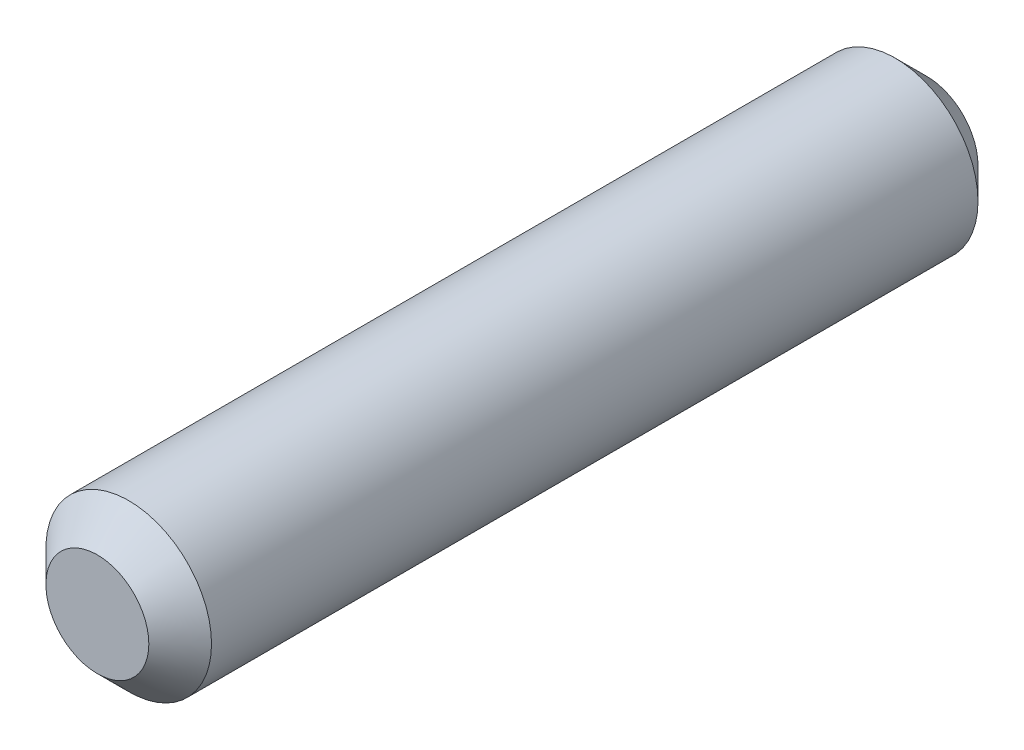
SolidWorks part; units mm, degrees
ref_plane "Front Plane" through (0, 0, 0) normal (0, 0, 1) x (1, 0, 0)
ref_plane "Top Plane" through (0, 0, 0) normal (0, 1, 0) x (1, 0, 0)
ref_plane "Right Plane" through (0, 0, 0) normal (1, 0, 0) x (0, 0, -1)
sketch "Sketch2" plane through (0, 0, 0) normal (0, 0, 1) x (1, 0, 0)
  circle A0 centre (0, 0) radius 1.585
  dimension "D1" = 3.17
extrude "Boss-Extrude1" add sketch "Sketch2" along normal mid plane 15.87
chamfer "Chamfer1" distance 0.6 angle 45 2 edges at (1.585, 0, -7.935) (1.585, 0, 7.935)
